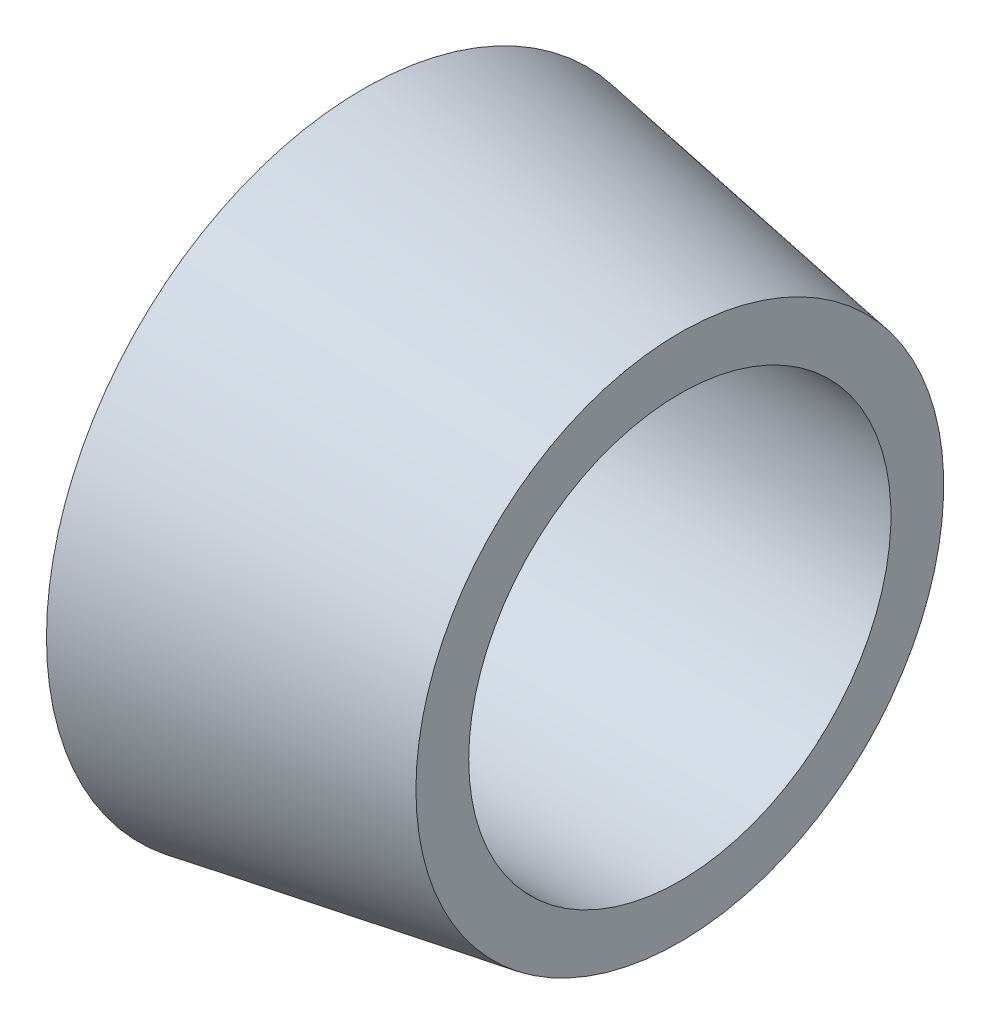
SolidWorks part; units mm, degrees
ref_plane "Płaszczyzna XY" through (0, 0, 0) normal (0, 0, 1) x (1, 0, 0)
ref_plane "Płaszczyzna XZ" through (0, 0, 0) normal (0, 1, 0) x (1, 0, 0)
ref_plane "Płaszczyzna YZ" through (0, 0, 0) normal (1, 0, 0) x (0, 0, -1)
sketch "Szkic1" plane through (0, 0, 0) normal (0, 0, 1) x (1, 0, 0)
  line L0 (0, 4) -> (0, 6)
  line L1 (0, 6) -> (6, 5)
  line L2 (6, 5) -> (6, 4)
  line L3 (6, 4) -> (0, 4)
  line L4 (0, 0) -> (11.0944, 0) construction
  dimension "D1" = 6
  dimension "D2" = 4
  dimension "D3" = 6
  dimension "D4" = 1
revolve "Obrót1" add sketch "Szkic1" angle 360 about L4
